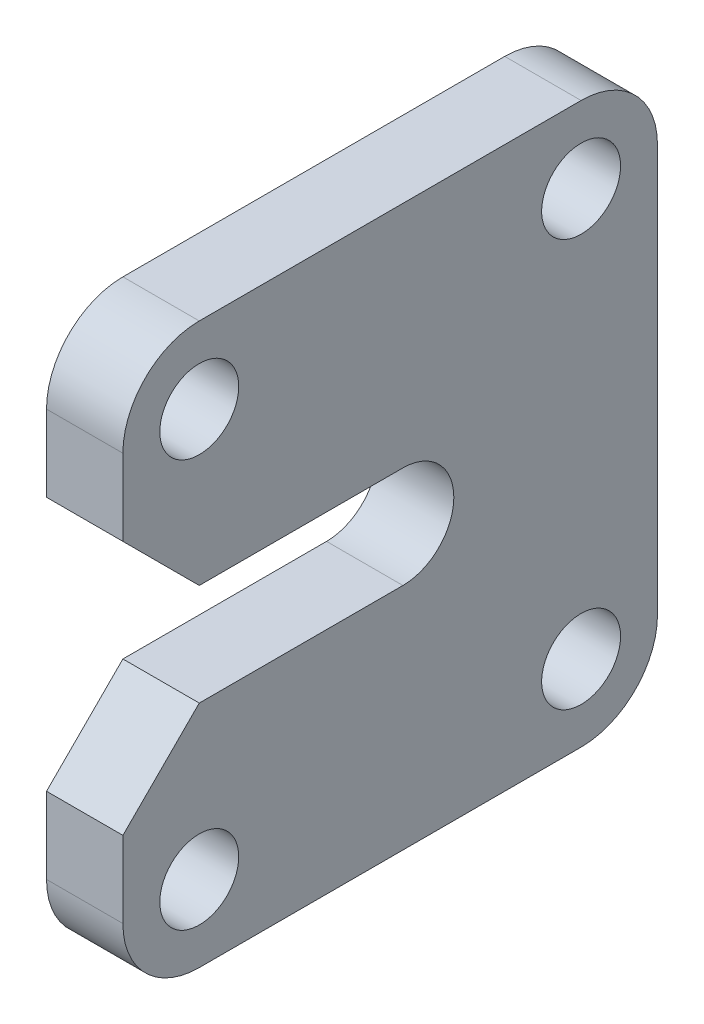
SolidWorks part; units mm, degrees
ref_plane "前视基准面" through (0, 0, 0) normal (0, 0, 1) x (1, 0, 0)
ref_plane "上视基准面" through (0, 0, 0) normal (0, 1, 0) x (1, 0, 0)
ref_plane "右视基准面" through (0, 0, 0) normal (1, 0, 0) x (0, 0, -1)
sketch "草图1" plane through (0, 0, 0) normal (1, 0, 0) x (0, 0, -1)
  line L0 (-89, 11) -> (-89, -11)
  line L1 (-92, -8) -> (-107, -8) construction
  line L2 (-92, -8) -> (-92, 8) construction
  line L3 (-92, 8) -> (-107, 8) construction
  line L4 (-107, -8) -> (-107, 8) construction
  line L5 (-92, -8) -> (-107, 8) construction
  line L6 (-92, 8) -> (-107, -8) construction
  line L7 (-89, 11) -> (-110, 11)
  line L8 (-89, -11) -> (-110, -11)
  line L9 (-110, 11) -> (-110, 5)
  line L10 (-110, 5) -> (-107, 2)
  line L11 (-107, 2) -> (-99, 2)
  line L12 (-99, -2) -> (-107, -2)
  line L13 (-107, -2) -> (-110, -5)
  line L14 (-110, -5) -> (-110, -11)
  circle A0 centre (-107, 8) radius 1.55
  circle A1 centre (-92, 8) radius 1.55
  circle A2 centre (-92, -8) radius 1.55
  circle A3 centre (-107, -8) radius 1.55
  arc A4 (-99, 2) -> (-99, -2) centre (-99, 0) cw
  point P0 (-99.5, 0)
  dimension "D1" = 3.1
  dimension "D8" = 45
  dimension "D9" = 2
  dimension "D12" = 3
  dimension "D2" = 16
  dimension "D3" = 15
  dimension "D4" = 92
  dimension "D5" = 3
  dimension "D6" = 3
  dimension "D7" = 3
  dimension "D10" = 10
  dimension "D11" = 3
extrude "凸台-拉伸1" add sketch "草图1" along normal mid plane 3
fillet "圆角1" radius 3 4 edges at (0, -11, 110) (0, -11, 89) (0, 11, 89) (0, 11, 110)
